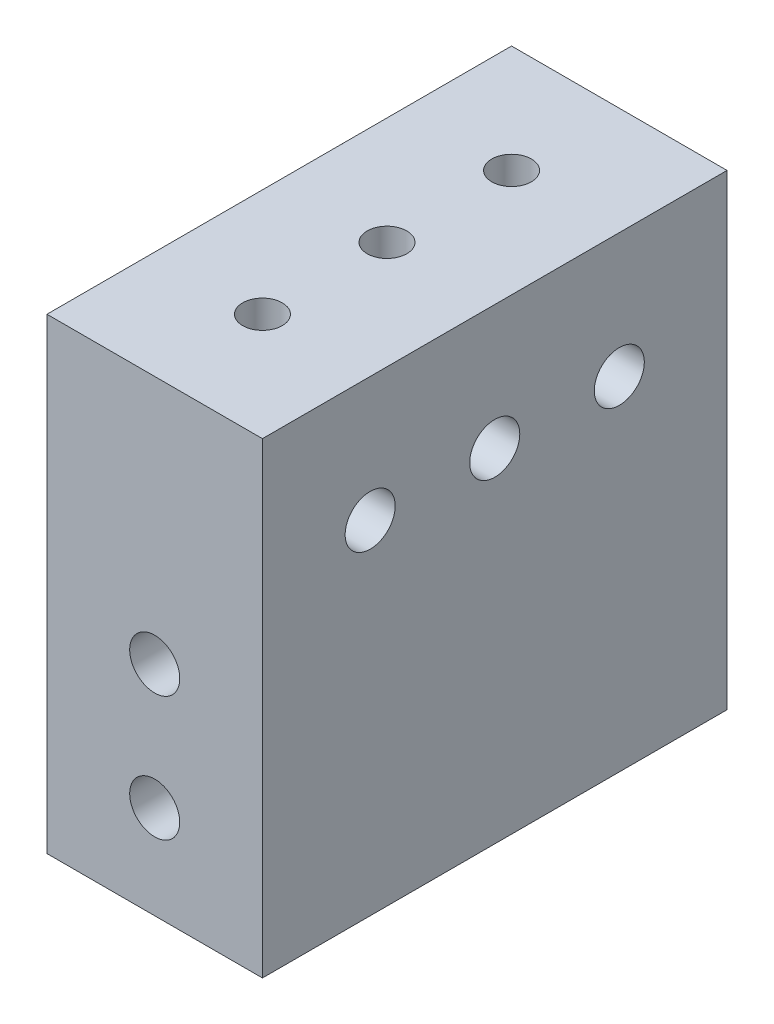
SolidWorks part; units mm, degrees
other "Markup1"
sketch "Sketch3" plane through (12.6365, 38.1, -23.749) normal (0.9027, 0.4189, -0.0984) x (-0.0151, -0.1977, -0.9801)
sketch "Sketch7" plane through (11.049, 23.8125, -23.749) normal (0.9027, 0.4189, -0.0984) x (-0.0151, -0.1977, -0.9801)
sketch "Sketch9" plane through (11.049, 23.8125, -23.749) normal (0.9027, 0.4189, -0.0984) x (-0.0151, -0.1977, -0.9801)
sketch "Sketch12" plane through (11.049, 23.8125, -23.749) normal (0.9027, 0.4189, -0.0984) x (-0.0151, -0.1977, -0.9801)
sketch "Sketch15" plane through (11.049, 23.8125, -23.749) normal (0.9027, 0.4189, -0.0984) x (-0.0151, -0.1977, -0.9801)
sketch "Sketch19" plane through (10.9855, 23.8125, -23.6855) normal (0.9027, 0.4189, -0.0984) x (-0.0151, -0.1977, -0.9801)
other "Markup2"
sketch "Sketch4" plane through (12.6365, 38.1, -23.749) normal (0.9027, 0.4189, -0.0984) x (-0.0151, -0.1977, -0.9801)
sketch "Sketch8" plane through (11.049, 23.8125, -23.749) normal (0.9027, 0.4189, -0.0984) x (-0.0151, -0.1977, -0.9801)
sketch "Sketch10" plane through (11.049, 23.8125, -23.749) normal (0.9027, 0.4189, -0.0984) x (-0.0151, -0.1977, -0.9801)
sketch "Sketch13" plane through (11.049, 23.8125, -23.749) normal (0.9027, 0.4189, -0.0984) x (-0.0151, -0.1977, -0.9801)
sketch "Sketch16" plane through (11.049, 23.8125, -23.749) normal (0.9027, 0.4189, -0.0984) x (-0.0151, -0.1977, -0.9801)
sketch "Sketch20" plane through (10.9855, 23.8125, -23.6855) normal (0.9027, 0.4189, -0.0984) x (-0.0151, -0.1977, -0.9801)
other "Markup3"
sketch "Sketch11" plane through (11.049, 23.8125, -23.749) normal (1, 0.0033, -0.0037) x (-0.003, -0.1893, -0.9819)
sketch "Sketch14" plane through (11.049, 23.8125, -23.749) normal (1, 0.0033, -0.0037) x (-0.003, -0.1893, -0.9819)
sketch "Sketch17" plane through (11.049, 23.8125, -23.749) normal (1, 0.0033, -0.0037) x (-0.003, -0.1893, -0.9819)
sketch "Sketch21" plane through (10.9855, 23.8125, -23.6855) normal (1, 0.0033, -0.0037) x (-0.003, -0.1893, -0.9819)
material "6061-T6 (SS)"
ref_plane "Front Plane" through (0, 0, 0) normal (0, 0, 1) x (1, 0, 0)
ref_plane "Top Plane" through (0, 0, 0) normal (0, 1, 0) x (1, 0, 0)
ref_plane "Right Plane" through (0, 0, 0) normal (1, 0, 0) x (0, 0, -1)
sketch "Sketch1" plane through (0, 0, 0) normal (0, 1, 0) x (1, 0, 0)
  line L0 (-12.573, 25.273) -> (12.573, 25.273)
  line L1 (-10.9855, -23.6855) -> (10.9855, -23.6855)
  line L2 (-10.9855, -23.6855) -> (-10.9855, 23.6855)
  line L3 (-10.9855, 23.6855) -> (10.9855, 23.6855)
  line L4 (10.9855, -23.6855) -> (10.9855, 23.6855)
  line L5 (-10.9855, -23.6855) -> (10.9855, 23.6855) construction
  line L6 (-10.9855, 23.6855) -> (10.9855, -23.6855) construction
  line L7 (12.573, -25.273) -> (12.573, 25.273)
  line L8 (-12.573, -25.273) -> (12.573, -25.273)
  line L9 (-12.573, -25.273) -> (-12.573, 25.273)
  point P0 (0, 0)
  dimension "D1" = 21.971
  dimension "D2" = 47.371
  dimension "D3" = 1.5875
extrude "Boss-Extrude1" add sketch "Sketch1" along normal mid plane 47.625 contours L1 L4 L3 L2
sketch "Sketch2" plane through (10.9855, 0, 0) normal (1, 0, 0) x (0, 0, -1)
  line L0 (-23.6855, 23.8125) -> (23.6855, 23.8125) construction
  line L4 (-25.4, -23.8125) -> (25.4, -23.8125) construction
  line L5 (-25.4, -23.8125) -> (-25.4, 23.8125) construction
  line L6 (-25.4, 23.8125) -> (25.4, 23.8125) construction
  line L7 (25.4, -23.8125) -> (25.4, 23.8125) construction
  line L8 (-25.4, -23.8125) -> (25.4, 23.8125) construction
  line L9 (-25.4, 23.8125) -> (25.4, -23.8125) construction
  circle A0 centre (-12.7, 11.1125) radius 2.5527
  circle A1 centre (0, 11.1125) radius 2.5527
  circle A2 centre (12.7, 11.1125) radius 2.5527
  point P6 (0, 0)
  dimension "D1" = 5.1054
  dimension "D2" = 50.8
  dimension "D4" = 25.4
  dimension "D5" = 12.7
  dimension "D6" = 38.1
  dimension "D7" = 12.7
  dimension "D8" = 12.7
  dimension "D9" = 12.7
extrude "Cut-Extrude1" cut sketch "Sketch2" against normal through all
sketch "Sketch5" plane through (0, 0, -23.6855) normal (0, 0, -1) x (-1, 0, 0)
  line L0 (10.9855, 23.8125) -> (-10.9855, 23.8125) construction
  line L1 (-12.7, -23.8125) -> (12.7, -23.8125) construction
  line L2 (-12.7, -23.8125) -> (-12.7, 23.8125) construction
  line L3 (-12.7, 23.8125) -> (12.7, 23.8125) construction
  line L4 (12.7, -23.8125) -> (12.7, 23.8125) construction
  line L5 (-12.7, -23.8125) -> (12.7, 23.8125) construction
  line L6 (-12.7, 23.8125) -> (12.7, -23.8125) construction
  circle A0 centre (0, -1.5875) radius 2.5527
  circle A2 centre (0, -14.2875) radius 2.5527
  point P0 (0, 0)
  dimension "D5" = 38.1
  dimension "D7" = 5.1054
  dimension "D8" = 5.1054
  dimension "D1" = 25.4
  dimension "D3" = 25.4
  dimension "D4" = 12.7
  dimension "D6" = 12.7
extrude "Cut-Extrude2" cut sketch "Sketch5" against normal through all
hole_wizard "#10-32 Tapped Hole1" positions "3DSketch1" profile "Sketch18" tap size "#10-32" standard "ANSI Inch" end condition through all
sketch3d "3DSketch1"
  line L0 (0, 23.8125, 23.6855) -> (0, 23.8125, -23.6855) construction
  line L1 (-10.9855, 23.8125, 23.6855) -> (10.9855, 23.8125, 23.6855) construction
  line L2 (-10.9855, 23.8125, -23.6855) -> (10.9855, 23.8125, -23.6855) construction
  point P0 (0, 23.8125, 12.7)
  point P5 (0, 23.8125, -12.7)
  point P9 (0, 23.8125, 0)
  dimension "D1" = 12.7
  dimension "D2" = 12.7
cosmetic thread "Hole Thread1" parameters "D1"=9.652, "D2"=4.826
cosmetic thread "Hole Thread2" parameters "D1"=9.652, "D2"=4.826
cosmetic thread "Hole Thread3" parameters "D1"=9.652, "D2"=4.826
sketch "Sketch18" plane through (0, 23.8125, 12.7) normal (1, 0, 0) x (0, 0, 1)
  line L0 (0, 0) -> (0, 47.625)
  line L1 (0, 47.625) -> (2.0193, 47.625)
  line L2 (2.0193, 47.625) -> (2.0193, 0)
  line L5 (2.0193, 0) -> (0, 0)
  line L11 (0, -6.35) -> (0, 107.95) construction
  dimension "Thru Tap Drill Dia." = 4.0386
  dimension "Thru Tap Drill Depth" = 47.625
